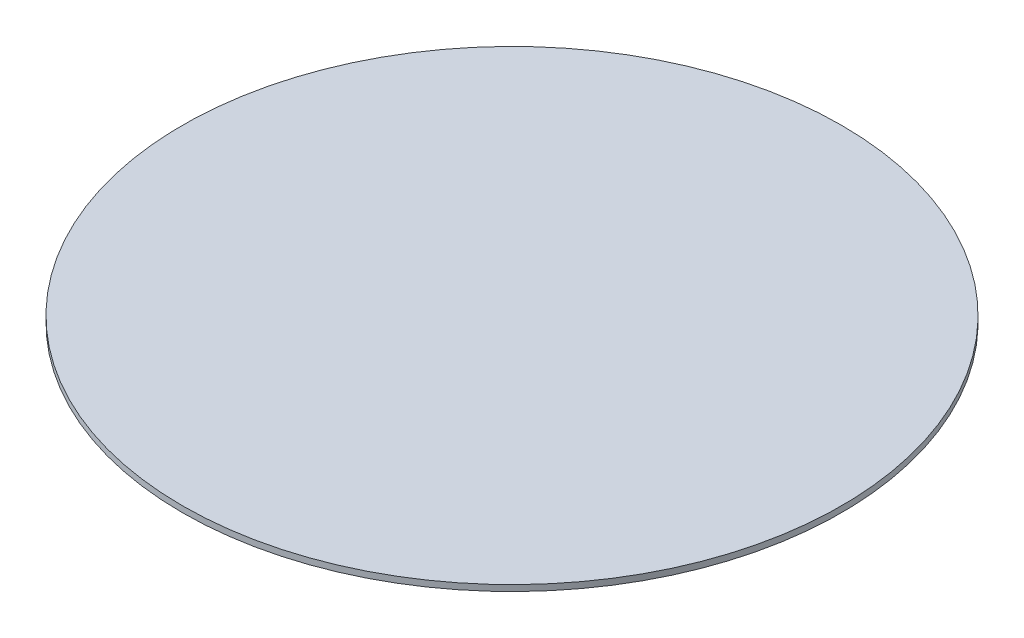
SolidWorks part; units mm, degrees
ref_plane "Plan de face" through (0, 0, 0) normal (0, 0, 1) x (1, 0, 0)
ref_plane "Plan de dessus" through (0, 0, 0) normal (0, 1, 0) x (1, 0, 0)
ref_plane "Plan de droite" through (0, 0, 0) normal (1, 0, 0) x (0, 0, -1)
sketch "Esquisse1" plane through (0, 129.0987, 0) normal (0, 1, 0) x (-1, 0, 0)
  circle A0 centre (322.9433, -81.5368) radius 60
  dimension "D1" = 120
extrude "Boss.-Extru.1" add sketch "Esquisse1" along normal blind 1.1
